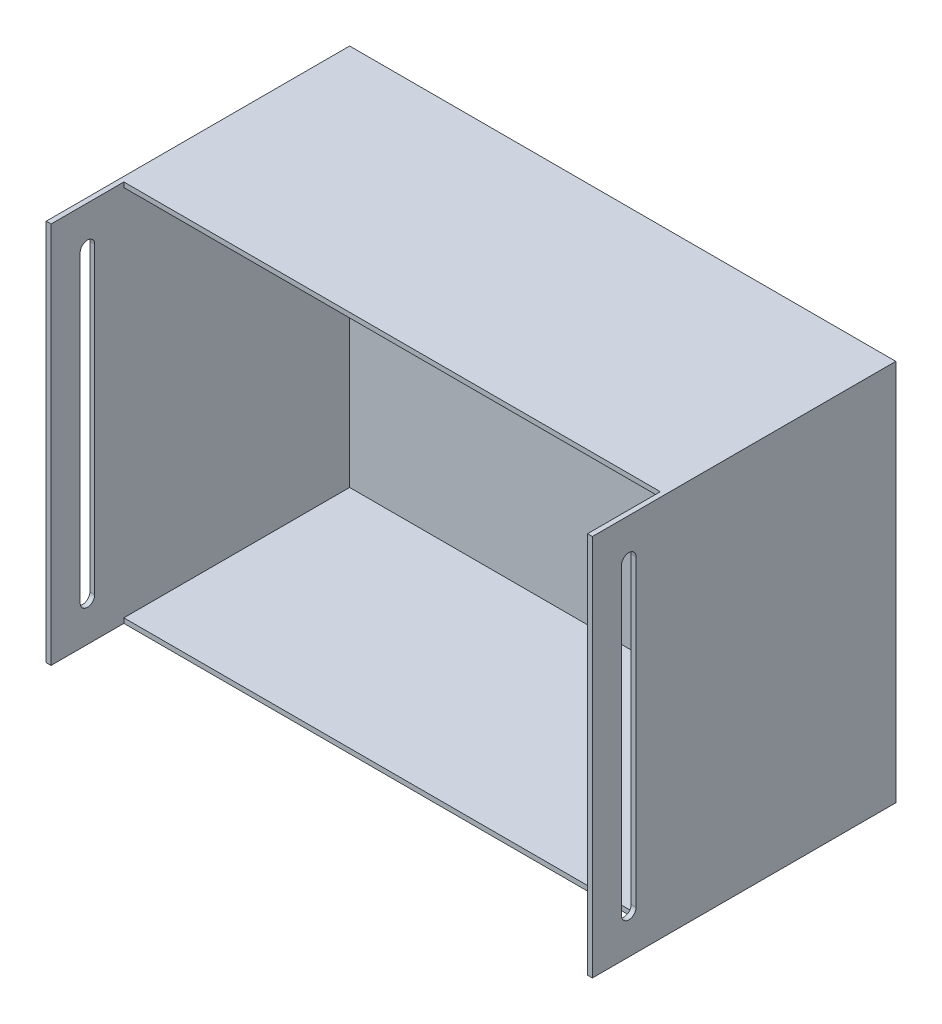
SolidWorks part; units mm, degrees
ref_plane "前视基准面" through (0, 0, 0) normal (0, 0, 1) x (1, 0, 0)
ref_plane "上视基准面" through (0, 0, 0) normal (0, 1, 0) x (1, 0, 0)
ref_plane "右视基准面" through (0, 0, 0) normal (1, 0, 0) x (0, 0, -1)
sketch "草图1" plane through (0, 0, 0) normal (0, 0, 1) x (1, 0, 0)
  line L1 (-225, -157.5) -> (225, -157.5)
  line L2 (-225, -157.5) -> (-225, 157.5)
  line L3 (-225, 157.5) -> (225, 157.5)
  line L4 (225, -157.5) -> (225, 157.5)
  line L5 (-225, -157.5) -> (225, 157.5) construction
  line L6 (-225, 157.5) -> (225, -157.5) construction
  point P0 (0, 0)
  dimension "D1" = 450
  dimension "D2" = 315
ref_plane "基准面1" through (0, 0, -300) normal (0, 0, 1) x (1, 0, 0)
ref_plane "基准面2" through (0, 0, -100) normal (0, 0, 1) x (1, 0, 0)
sketch "草图3" plane through (0, 0, -100) normal (0, 0, 1) x (1, 0, 0)
  circle A0 centre (0, 0) radius 190
extrude "凸台-拉伸1" add sketch "草图1" against normal blind 250 contours L4 L3 L2 L1
shell "抽壳3" thickness 4
sketch "草图4" plane through (0, -157.5, 0) normal (0, -1, 0) x (1, 0, 0)
  line L0 (0, 0) -> (0, -30) construction
  line L1 (-221, -60) -> (221, -60)
  line L2 (-221, -60) -> (-221, 0)
  line L3 (-221, 0) -> (221, 0)
  line L4 (221, -60) -> (221, 0)
  line L5 (-221, -60) -> (221, 0) construction
  line L6 (-221, 0) -> (221, -60) construction
  line L7 (225, -250) -> (225, 0) construction
  line L8 (-225, 0) -> (225, 0) construction
  point P0 (0, -30)
  dimension "D1" = 4
  dimension "D2" = 60
extrude "切除-拉伸1" cut sketch "草图4" against normal through all
sketch "草图5" plane through (225, 0, 0) normal (1, 0, 0) x (0, 0, -1)
  line L0 (30, 157.5) -> (30, -157.5) construction
  line L4 (250, 157.5) -> (0, 157.5) construction
  line L5 (250, -157.5) -> (0, -157.5) construction
  line L6 (0, -157.5) -> (0, 157.5) construction
  line L7 (0, 0) -> (62.1143, 0) construction
  line L8 (30, 125) -> (30, -125) construction
  line L10 (36, 125) -> (36, -125)
  line L11 (24, 125) -> (24, -125)
  arc A0 (36, 125) -> (24, 125) centre (30, 125) ccw
  arc A1 (24, -125) -> (36, -125) centre (30, -125) ccw
  point P14 (30, 0)
  dimension "D2" = 250
  dimension "D3" = 6
  dimension "D1" = 30
extrude "切除-拉伸2" cut sketch "草图5" against normal through all
